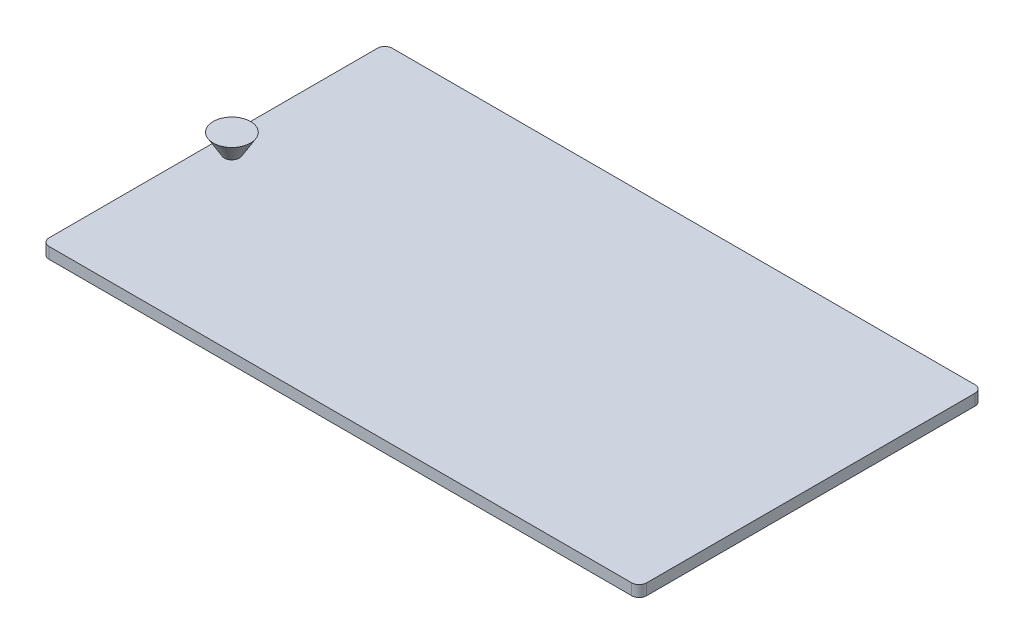
SolidWorks part; units mm, degrees
ref_plane "Front Plane" through (0, 0, 0) normal (0, 0, 1) x (1, 0, 0)
ref_plane "Top Plane" through (0, 0, 0) normal (0, 1, 0) x (1, 0, 0)
ref_plane "Right Plane" through (0, 0, 0) normal (1, 0, 0) x (0, 0, -1)
sketch "Sketch1" plane through (0, 0, 0) normal (0, 1, 0) x (1, 0, 0)
  line L1 (-78, 45.95) -> (78, 45.95)
  line L2 (-80, 43.95) -> (-80, -43.95)
  line L3 (-78, -45.95) -> (78, -45.95)
  line L4 (80, 43.95) -> (80, -43.95)
  line L5 (-80, 45.95) -> (80, -45.95) construction
  line L6 (-80, -45.95) -> (80, 45.95) construction
  arc A0 (-78, 45.95) -> (-80, 43.95) centre (-78, 43.95) ccw
  arc A1 (-78, -45.95) -> (-80, -43.95) centre (-78, -43.95) cw
  arc A2 (80, 43.95) -> (78, 45.95) centre (78, 43.95) ccw
  arc A3 (78, -45.95) -> (80, -43.95) centre (78, -43.95) ccw
  point P0 (0, 0)
  dimension "D3" = 2
  dimension "D4" = 2
  dimension "D5" = 2
  dimension "D6" = 2
  dimension "D1" = 160
  dimension "D2" = 91.9
extrude "Boss-Extrude3" add sketch "Sketch1" along normal blind 3
sketch "Sketch2" plane through (0, 3, 0) normal (0, 1, 0) x (1, 0, 0)
  line L0 (-80, 43.95) -> (-80, -43.95) construction
  line L2 (78, 45.95) -> (-78, 45.95) construction
  circle A0 centre (-75, 0) radius 2
  dimension "D1" = 4
  dimension "D2" = 5
  dimension "D3" = 45.95
ref_plane "Plane1" through (0, 8, 0) normal (0, 1, 0) x (1, 0, 0)
sketch "Sketch3" plane through (0, 8, 0) normal (0, 1, 0) x (1, 0, 0)
  circle A0 centre (-75, 0) radius 5
  dimension "D1" = 10
loft "Loft1" add profiles "Sketch3", "Sketch2"
